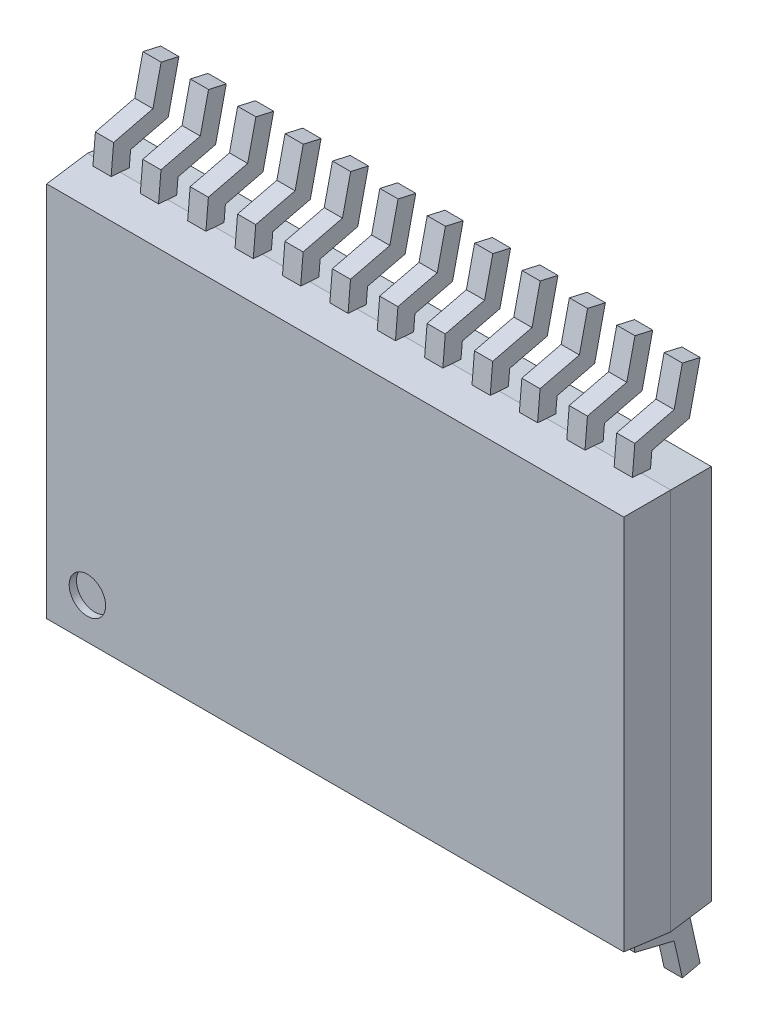
SolidWorks part; units mm, degrees
ref_plane "Front Plane" through (0, 0, 0) normal (0, 0, 1) x (1, 0, 0)
ref_plane "Top Plane" through (0, 0, 0) normal (0, 1, 0) x (1, 0, 0)
ref_plane "Right Plane" through (0, 0, 0) normal (1, 0, 0) x (0, 0, -1)
sketch "Sketch1" plane through (0, 0, 0) normal (0, 0, 1) x (1, 0, 0)
  line L1 (0, 0) -> (8, 0)
  line L2 (0, 0) -> (0, 5.25)
  line L3 (0, 5.25) -> (8, 5.25)
  line L4 (8, 0) -> (8, 5.25)
  dimension "D1" = 8
  dimension "D2" = 5.25
extrude "Boss-Extrude1" add sketch "Sketch1" along normal blind 0.6 draft 4
mirror "Mirror1" about plane through (0, 0, 0) normal (0, 0, 1) of "Boss-Extrude1"
ref_plane "Plane1" through (0.325, 0, 0) normal (1, 0, 0) x (0, 0, -1)
sketch "Sketch5" plane through (0.325, 0, 0) normal (1, 0, 0) x (0, 0, -1)
  line L0 (0, 0) -> (0.0262, -0.2989)
  line L1 (0.0262, -0.2989) -> (0.5535, -0.4276)
  line L2 (0.5535, -0.4276) -> (0.6832, -1)
  dimension "D1" = 1
extrude "Extrude-Thin1" add sketch "Sketch5" along normal mid plane 0.25 thin thin type mid plane wall 0.25
pattern_linear "LPattern1" count 12 spacing 0.65 along (1, 0, 0) of "Extrude-Thin1"
sketch "Sketch6" plane through (0, 0, 0) normal (0, 0, 1) x (1, 0, 0)
  circle A0 centre (0.6, 0.6) radius 0.25
extrude "Cut-Extrude2" cut sketch "Sketch6" along direction (0, 0, 1) on the side of the normal blind 0.2 from offset 0.5
ref_plane "Plane2" through (0, 2.625, 0) normal (0, 1, 0) x (1, 0, 0)
mirror "Mirror2" about plane through (0, 2.625, 0) normal (0, 1, 0) of "LPattern1", "Extrude-Thin1"
